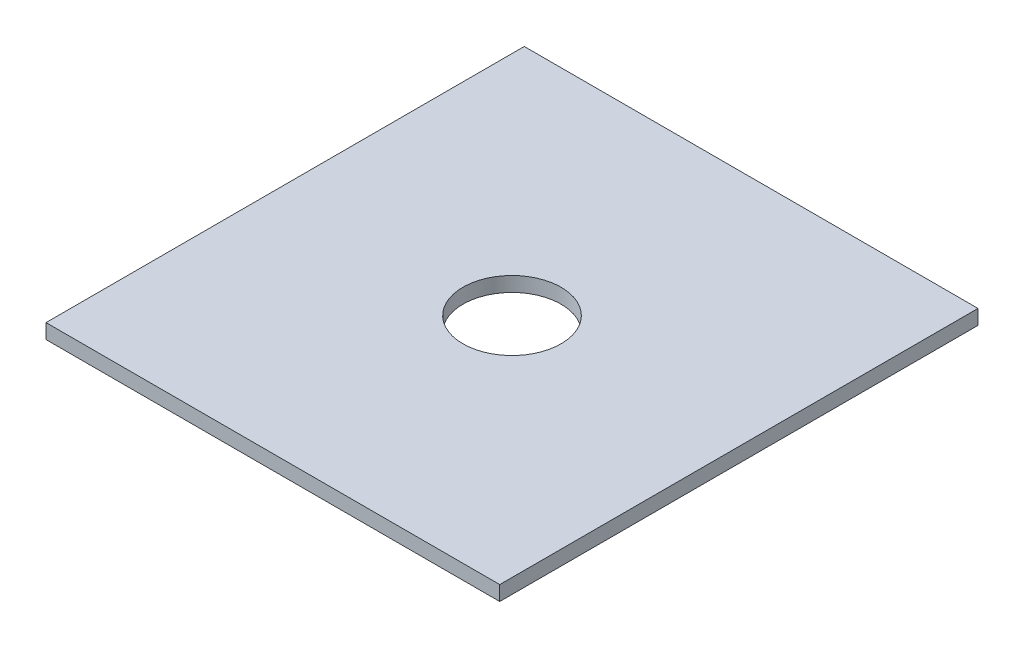
SolidWorks part; units mm, degrees
ref_plane "Front Plane" through (0, 0, 0) normal (0, 0, 1) x (1, 0, 0)
ref_plane "Top Plane" through (0, 0, 0) normal (0, 1, 0) x (1, 0, 0)
ref_plane "Right Plane" through (0, 0, 0) normal (1, 0, 0) x (0, 0, -1)
sketch "Sketch1" plane through (0, 0, 0) normal (0, 1, 0) x (1, 0, 0)
  line L0 (-112.0122, -187.8659) -> (-112.0122, 170.0305) construction
  line L1 (-204.5122, 107.0122) -> (-19.5122, 107.0122)
  line L2 (-204.5122, 107.0122) -> (-204.5122, -87.9878)
  line L3 (-204.5122, -87.9878) -> (-19.5122, -87.9878)
  line L4 (-19.5122, 107.0122) -> (-19.5122, -87.9878)
  line L5 (-204.5122, 9.5122) -> (-19.5122, 9.5122) construction
  circle A0 centre (-112.0122, 9.5122) radius 20
  dimension "D1" = 195
  dimension "D2" = 185
extrude "Boss-Extrude1" add sketch "Sketch1" along normal blind 6
